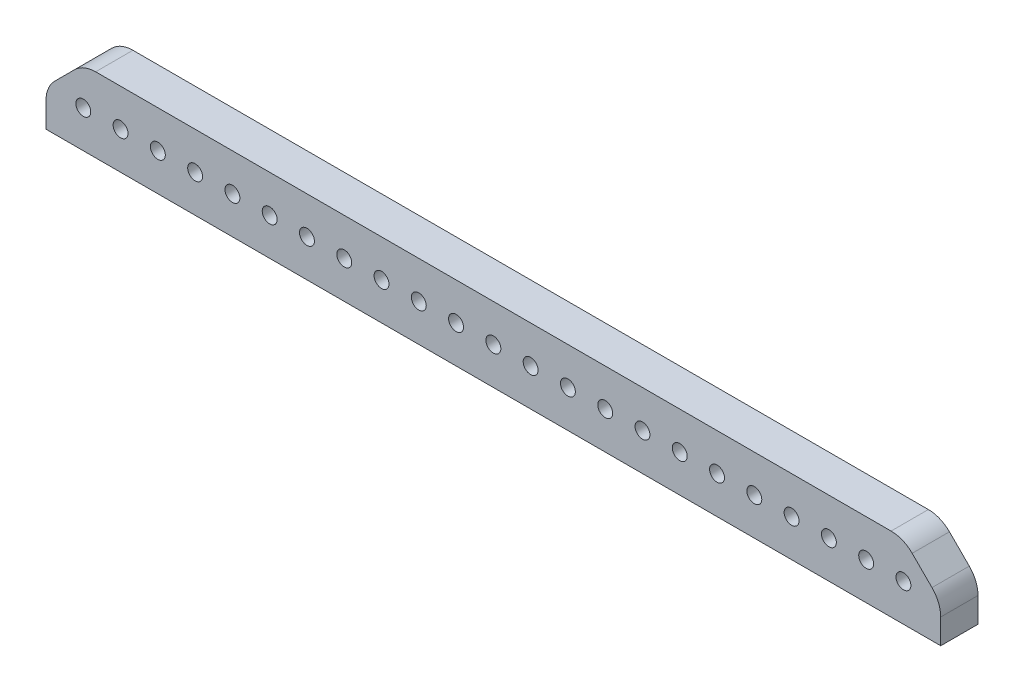
SolidWorks part; units mm, degrees
ref_plane "Front Plane" through (0, 0, 0) normal (0, 0, 1) x (1, 0, 0)
ref_plane "Top Plane" through (0, 0, 0) normal (0, 1, 0) x (1, 0, 0)
ref_plane "Right Plane" through (0, 0, 0) normal (1, 0, 0) x (0, 0, -1)
sketch "Sketch1" plane through (0, 0, 0) normal (0, 0, 1) x (1, 0, 0)
  line L1 (-76.2, -6.35) -> (76.2, -6.35)
  line L2 (-76.2, -6.35) -> (-76.2, 6.35)
  line L3 (-76.2, 6.35) -> (76.2, 6.35)
  line L4 (76.2, -6.35) -> (76.2, 6.35)
  line L5 (-76.2, -6.35) -> (76.2, 6.35) construction
  line L6 (-76.2, 6.35) -> (76.2, -6.35) construction
  point P0 (0, 0)
  dimension "D1" = 152.4
  dimension "D2" = 12.7
extrude "Boss-Extrude1" add sketch "Sketch1" along normal blind 6.35
sketch "Sketch2" plane through (0, 0, 6.35) normal (0, 0, 1) x (1, 0, 0)
  circle A0 centre (0, 0) radius 1.27
  dimension "D1" = 2.54
extrude "Cut-Extrude1" cut sketch "Sketch2" against normal through all
pattern_linear "LPattern1" count 12 spacing 6.35 along (1, 0, 0) count 12 spacing 6.35 along (-1, 0, 0) of "Cut-Extrude1"
chamfer "Chamfer1" distance 6.35 angle 45 2 edges at (76.2, 6.35, 3.175) (-76.2, 6.35, 3.175)
fillet "Fillet1" radius 5.08 4 edges at (-69.85, 6.35, 3.175) (-76.2, 0, 3.175) (69.85, 6.35, 3.175) (76.2, 0, 3.175)
